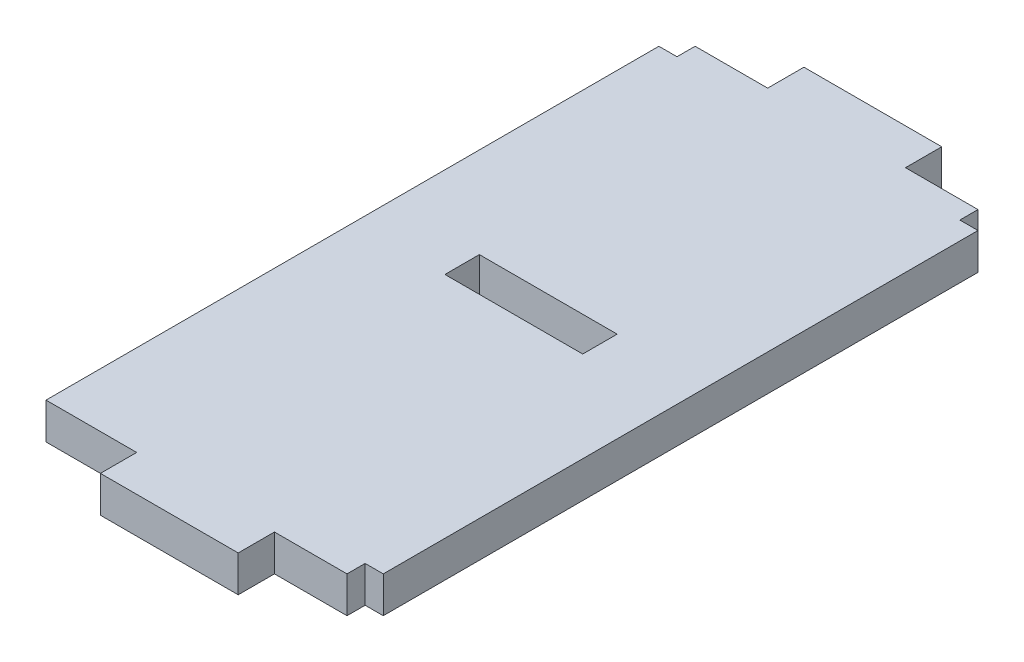
SolidWorks part; units mm, degrees
ref_plane "前视基准面" through (0, 0, 0) normal (0, 0, 1) x (1, 0, 0)
ref_plane "上视基准面" through (0, 0, 0) normal (0, 1, 0) x (1, 0, 0)
ref_plane "右视基准面" through (0, 0, 0) normal (1, 0, 0) x (0, 0, -1)
sketch "草图1" plane through (0, 0, 0) normal (0, 1, 0) x (1, 0, 0)
  line L0 (-2, -2) -> (19.6, -2) construction
  line L1 (0, 0) -> (17.6, 0)
  line L2 (0, 0) -> (0, 34.8)
  line L3 (0, 34.8) -> (17.6, 34.8)
  line L4 (17.6, 0) -> (17.6, 34.8)
  line L5 (19.6, -2) -> (19.6, 36.8) construction
  line L6 (-2, 36.8) -> (19.6, 36.8) construction
  line L7 (-2, -2) -> (-2, 36.8) construction
  line L8 (12.6, 5) -> (12.6, 29.8) construction
  line L9 (5, 29.8) -> (12.6, 29.8) construction
  line L10 (5, 5) -> (5, 29.8) construction
  line L11 (5, 5) -> (12.6, 5) construction
  line L12 (12.6, 5) -> (12.6, -4.6272) construction
  line L13 (5, 5) -> (5, -2) construction
  line L14 (-6.6019, 17) -> (28.6178, 17) construction
  line L15 (5, 0) -> (12.6, 0)
  line L16 (5, 0) -> (5, -2)
  line L17 (5, -2) -> (12.6, -2)
  line L18 (12.6, 0) -> (12.6, -2)
  line L19 (5, 36.8) -> (12.6, 36.8)
  line L20 (5, 36.8) -> (5, 34.8)
  line L21 (5, 34.8) -> (12.6, 34.8)
  line L22 (12.6, 36.8) -> (12.6, 34.8)
  line L23 (-6.6019, 18.9) -> (28.6178, 18.9) construction
  line L24 (-6.6019, 17) -> (28.6178, 17) construction
  line L25 (5, 18.9) -> (12.6, 18.9)
  line L26 (5, 18.9) -> (5, 17)
  line L27 (5, 17) -> (12.6, 17)
  line L28 (12.6, 18.9) -> (12.6, 17)
  line L30 (0, 34.8) -> (1, 34.8)
  line L31 (0, 34.8) -> (0, 33.8)
  line L32 (0, 33.8) -> (1, 33.8)
  line L33 (1, 34.8) -> (1, 33.8)
  line L34 (17.6, 34.8) -> (16.6, 34.8)
  line L35 (17.6, 34.8) -> (17.6, 33.8)
  line L36 (17.6, 33.8) -> (16.6, 33.8)
  line L37 (16.6, 34.8) -> (16.6, 33.8)
  line L38 (17.6, 0) -> (16.6, 0)
  line L39 (17.6, 0) -> (17.6, 1)
  line L40 (17.6, 1) -> (16.6, 1)
  line L41 (16.6, 0) -> (16.6, 1)
  dimension "D1" = 2
  dimension "D2" = 5
  dimension "D3" = 1.9
extrude "凸台-拉伸1" add sketch "草图1" along normal blind 2 contours L1 L4 L3 L2 L25 L28 L27 L26 | L18 L1 L16 L17 | L22 L19 L20 L3
